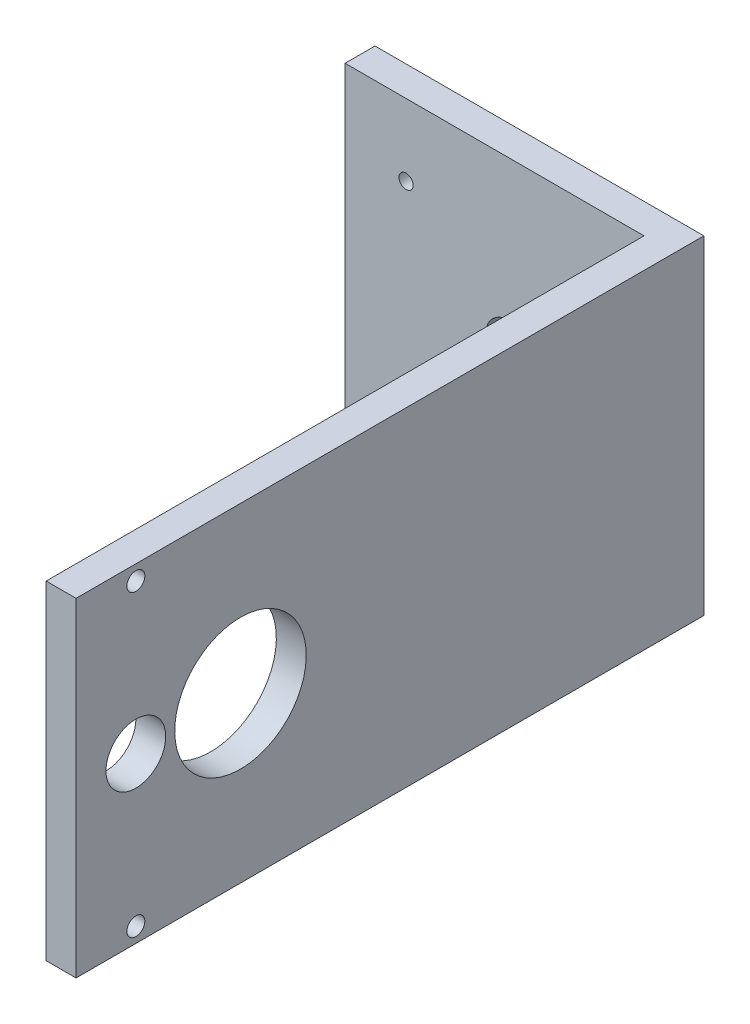
SolidWorks part; units mm, degrees
ref_plane "Ön Düzlem" through (0, 0, 0) normal (0, 0, 1) x (1, 0, 0)
ref_plane "Üst Düzlem" through (0, 0, 0) normal (0, 1, 0) x (1, 0, 0)
ref_plane "Sağ Düzlem" through (0, 0, 0) normal (1, 0, 0) x (0, 0, -1)
sketch "Sketch1" plane through (0, 0, 0) normal (0, 0, 1) x (1, 0, 0)
  line L1 (-27.5, 27.5) -> (27.5, 27.5)
  line L2 (-27.5, 27.5) -> (-27.5, -27.5)
  line L3 (-27.5, -27.5) -> (27.5, -27.5)
  line L4 (27.5, 27.5) -> (27.5, -27.5)
  line L5 (-27.5, 27.5) -> (27.5, -27.5) construction
  line L6 (-27.5, -27.5) -> (27.5, 27.5) construction
  point P0 (0, 0)
  dimension "D1" = 55
  dimension "D2" = 55
extrude "Boss-Extrude1" add sketch "Sketch1" along normal blind 5
sketch "Sketch2" plane through (0, 0, 5) normal (0, 0, 1) x (1, 0, 0)
  line L0 (-27.5, -27.5) -> (27.5, -27.5) construction
  line L1 (27.5, 27.5) -> (22.5, 27.5)
  line L2 (27.5, 27.5) -> (27.5, -27.5)
  line L3 (27.5, -27.5) -> (22.5, -27.5)
  line L4 (22.5, 27.5) -> (22.5, -27.5)
  dimension "D1" = 5
extrude "Boss-Extrude2" add sketch "Sketch2" along normal blind 100
sketch "Sketch3" plane through (27.5, 0, 0) normal (1, 0, 0) x (0, 0, -1)
  line L0 (-105, -27.5) -> (-105, 27.5) construction
  line L1 (-105, -27.5) -> (0, -27.5) construction
  circle A0 centre (-95, 0) radius 5
  circle A1 centre (-95, 25) radius 1.5
  circle A2 centre (-95, -25) radius 1.5
  circle A3 centre (-77.5, 0) radius 11
  dimension "D1" = 3
  dimension "D2" = 3
  dimension "D5" = 10
  dimension "D7" = 10
  dimension "D8" = 22
  dimension "D3" = 50
  dimension "D4" = 2.5
  dimension "D6" = 10
  dimension "D9" = 17.5
extrude "Cut-Extrude1" cut sketch "Sketch3" against normal up to next
sketch "Sketch4" plane through (0, 0, 5) normal (0, 0, 1) x (1, 0, 0)
  circle A0 centre (0, 0) radius 4
  dimension "D1" = 8
extrude "Cut-Extrude2" cut sketch "Sketch4" against normal up to next
hole_wizard "#4-48 Tapped Hole1" positions "Sketch7" profile "Sketch6" tap size "#4-48" standard "ANSI Inch"
sketch "Sketch7" plane through (0, 0, 5) normal (0, 0, 1) x (1, 0, 0)
  point P0 (-17.3, 15.5)
  point P3 (-17.3, -15.5)
sketch "Sketch6" plane through (-17.3, 15.5, 5) normal (1, 0, 0) x (0, -1, 0)
  line L0 (0, 0) -> (0, 4.2135)
  line L1 (0, 4.2135) -> (1.1874, 3.5)
  line L2 (1.1874, 3.5) -> (1.1874, 0)
  line L5 (1.1874, 0) -> (0, 0)
  line L10 (0, 4.2135) -> (-1.1875, 3.5) construction
  line L11 (0, -6.35) -> (0, 107.95) construction
  dimension "Tap Drill Dia." = 2.3749
  dimension "Tap Drill Depth" = 3.5
  dimension "Drill Angle" = 118
